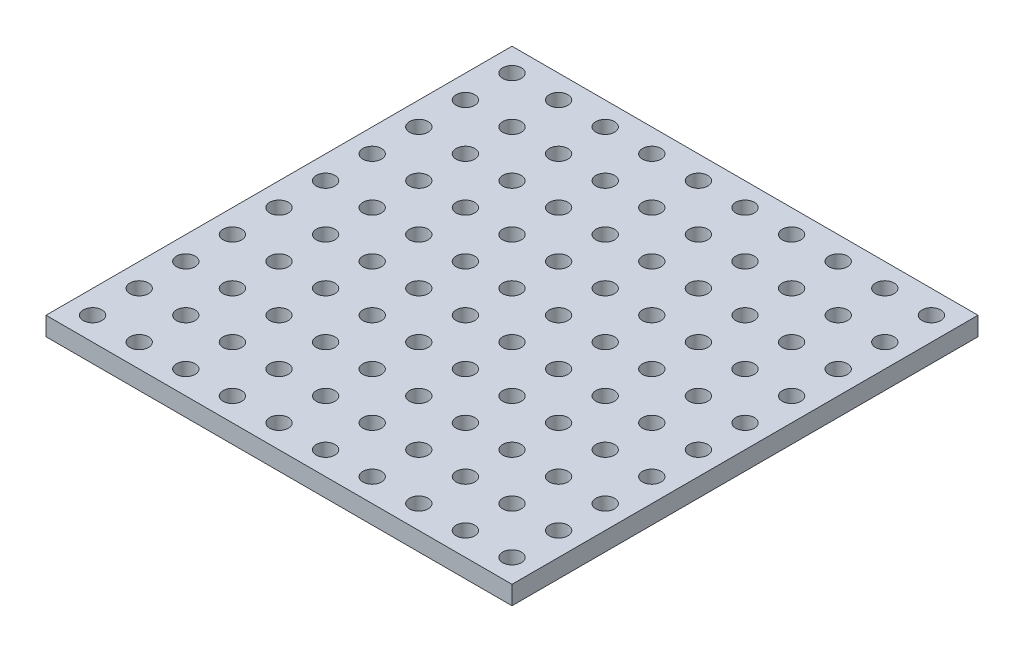
SolidWorks part; units mm, degrees
material "AISI 1020"
ref_plane "Plano frontal" through (0, 0, 0) normal (0, 0, 1) x (1, 0, 0)
ref_plane "Plano superior" through (0, 0, 0) normal (0, 1, 0) x (1, 0, 0)
ref_plane "Plano direito" through (0, 0, 0) normal (1, 0, 0) x (0, 0, -1)
sketch "Esboço1" plane through (0, 0, 0) normal (0, 1, 0) x (1, 0, 0)
  line L1 (-250, -250) -> (250, -250)
  line L2 (-250, -250) -> (-250, 250)
  line L3 (-250, 250) -> (250, 250)
  line L4 (250, -250) -> (250, 250)
  line L5 (-250, -250) -> (250, 250) construction
  line L6 (-250, 250) -> (250, -250) construction
  point P0 (0, 0)
  dimension "D1" = 500
extrude "Ressalto-extrusão1" add sketch "Esboço1" along normal blind 20
sketch "Esboço2" plane through (0, 20, 0) normal (0, 1, 0) x (1, 0, 0)
  line L0 (-250, 250) -> (-250, -250) construction
  line L1 (250, 250) -> (-250, 250) construction
  circle A0 centre (-225, 225) radius 10
  circle A1 centre (-175, 225) radius 10
  circle A2 centre (-125, 225) radius 10
  circle A3 centre (-75, 225) radius 10
  circle A4 centre (-25, 225) radius 10
  circle A5 centre (25, 225) radius 10
  circle A6 centre (75, 225) radius 10
  circle A7 centre (125, 225) radius 10
  circle A8 centre (175, 225) radius 10
  circle A9 centre (225, 225) radius 10
  circle A10 centre (-175, 175) radius 10
  circle A11 centre (-125, 175) radius 10
  circle A12 centre (-75, 175) radius 10
  circle A13 centre (-25, 175) radius 10
  circle A14 centre (25, 175) radius 10
  circle A15 centre (75, 175) radius 10
  circle A16 centre (125, 175) radius 10
  circle A17 centre (175, 175) radius 10
  circle A18 centre (225, 175) radius 10
  circle A19 centre (-175, 125) radius 10
  circle A20 centre (-125, 125) radius 10
  circle A21 centre (-75, 125) radius 10
  circle A22 centre (-25, 125) radius 10
  circle A23 centre (25, 125) radius 10
  circle A24 centre (75, 125) radius 10
  circle A25 centre (125, 125) radius 10
  circle A26 centre (175, 125) radius 10
  circle A27 centre (225, 125) radius 10
  circle A28 centre (-175, 75) radius 10
  circle A29 centre (-125, 75) radius 10
  circle A30 centre (-75, 75) radius 10
  circle A31 centre (-25, 75) radius 10
  circle A32 centre (25, 75) radius 10
  circle A33 centre (75, 75) radius 10
  circle A34 centre (125, 75) radius 10
  circle A35 centre (175, 75) radius 10
  circle A36 centre (225, 75) radius 10
  circle A37 centre (-175, 25) radius 10
  circle A38 centre (-125, 25) radius 10
  circle A39 centre (-75, 25) radius 10
  circle A40 centre (-25, 25) radius 10
  circle A41 centre (25, 25) radius 10
  circle A42 centre (75, 25) radius 10
  circle A43 centre (125, 25) radius 10
  circle A44 centre (175, 25) radius 10
  circle A45 centre (225, 25) radius 10
  circle A46 centre (-175, -25) radius 10
  circle A47 centre (-125, -25) radius 10
  circle A48 centre (-75, -25) radius 10
  circle A49 centre (-25, -25) radius 10
  circle A50 centre (25, -25) radius 10
  circle A51 centre (75, -25) radius 10
  circle A52 centre (125, -25) radius 10
  circle A53 centre (175, -25) radius 10
  circle A54 centre (225, -25) radius 10
  circle A55 centre (-175, -75) radius 10
  circle A56 centre (-125, -75) radius 10
  circle A57 centre (-75, -75) radius 10
  circle A58 centre (-25, -75) radius 10
  circle A59 centre (25, -75) radius 10
  circle A60 centre (75, -75) radius 10
  circle A61 centre (125, -75) radius 10
  circle A62 centre (175, -75) radius 10
  circle A63 centre (225, -75) radius 10
  circle A64 centre (-175, -125) radius 10
  circle A65 centre (-125, -125) radius 10
  circle A66 centre (-75, -125) radius 10
  circle A67 centre (-25, -125) radius 10
  circle A68 centre (25, -125) radius 10
  circle A69 centre (75, -125) radius 10
  circle A70 centre (125, -125) radius 10
  circle A71 centre (175, -125) radius 10
  circle A72 centre (225, -125) radius 10
  circle A73 centre (-175, -175) radius 10
  circle A74 centre (-125, -175) radius 10
  circle A75 centre (-75, -175) radius 10
  circle A76 centre (-25, -175) radius 10
  circle A77 centre (25, -175) radius 10
  circle A78 centre (75, -175) radius 10
  circle A79 centre (125, -175) radius 10
  circle A80 centre (175, -175) radius 10
  circle A81 centre (225, -175) radius 10
  circle A82 centre (-175, -225) radius 10
  circle A83 centre (-125, -225) radius 10
  circle A84 centre (-75, -225) radius 10
  circle A85 centre (-25, -225) radius 10
  circle A86 centre (25, -225) radius 10
  circle A87 centre (75, -225) radius 10
  circle A88 centre (125, -225) radius 10
  circle A89 centre (175, -225) radius 10
  circle A90 centre (225, -225) radius 10
  circle A91 centre (-225, 175) radius 10
  circle A92 centre (-225, 125) radius 10
  circle A93 centre (-225, 75) radius 10
  circle A94 centre (-225, 25) radius 10
  circle A95 centre (-225, -25) radius 10
  circle A96 centre (-225, -75) radius 10
  circle A97 centre (-225, -125) radius 10
  circle A98 centre (-225, -175) radius 10
  circle A99 centre (-225, -225) radius 10
  dimension "D1" = 20
  dimension "D2" = 25
  dimension "D3" = 25
  dimension "D4" = 10
  dimension "D5" = 10
extrude "Corte-extrusão1" cut sketch "Esboço2" against normal through all
